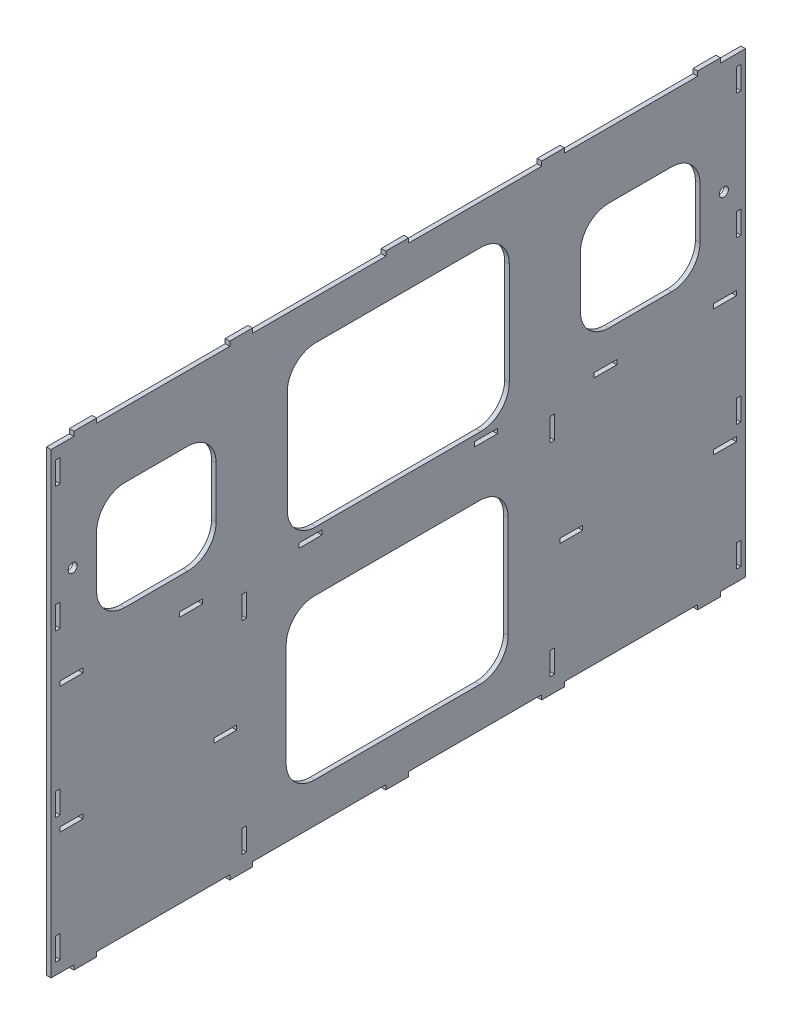
SolidWorks part; units mm, degrees
ref_plane "Front Plane" through (0, 0, 0) normal (0, 0, 1) x (1, 0, 0)
ref_plane "Top Plane" through (0, 0, 0) normal (0, 1, 0) x (1, 0, 0)
ref_plane "Right Plane" through (0, 0, 0) normal (1, 0, 0) x (0, 0, -1)
sketch "Sketch1" plane through (0, 0, 0) normal (1, 0, 0) x (0, 0, -1)
  line L0 (-96.5647, -205) -> (-96.5647, 335.0044) construction
  line L1 (-361.6328, 35) -> (431.039, 35) construction
  line L2 (-401.5647, -166) -> (-381.5647, -166)
  line L3 (-381.5647, 240) -> (-361.5647, 240)
  line L4 (-401.5647, 236) -> (-401.5647, -166)
  line L5 (-381.5647, -170) -> (-361.5647, -170)
  line L7 (208.4353, 236) -> (208.4353, -166)
  line L8 (180.4353, -55) -> (180.4353, -59)
  line L9 (-381.5647, -166) -> (-381.5647, -170)
  line L10 (-361.5647, -166) -> (-361.5647, -170)
  line L11 (-361.5647, -166) -> (-244.5647, -166)
  line L12 (-244.5647, -166) -> (-244.5647, -170)
  line L13 (-224.5647, -166) -> (-224.5647, -170)
  line L14 (-224.5647, -166) -> (-107.5647, -166)
  line L15 (-107.5647, -166) -> (-107.5647, -170)
  line L16 (-87.5647, -170) -> (-87.5647, -166)
  line L17 (-87.5647, -166) -> (29.4353, -166)
  line L18 (29.4353, -166) -> (29.4353, -170)
  line L19 (49.4353, -170) -> (49.4353, -166)
  line L20 (49.4353, -166) -> (166.4353, -166)
  line L21 (166.4353, -166) -> (166.4353, -170)
  line L28 (166.4353, -170) -> (186.4353, -170)
  line L29 (29.4353, -170) -> (49.4353, -170)
  line L30 (-107.5647, -170) -> (-87.5647, -170)
  line L31 (-244.5647, -170) -> (-224.5647, -170)
  line L34 (186.4353, 236) -> (186.4353, 240)
  line L35 (208.4353, 236) -> (186.4353, 236)
  line L37 (49.4353, 236) -> (166.4353, 236)
  line L38 (49.4353, 240) -> (49.4353, 236)
  line L39 (29.4353, 236) -> (29.4353, 240)
  line L40 (-87.5647, 236) -> (29.4353, 236)
  line L41 (-87.5647, 240) -> (-87.5647, 236)
  line L42 (-107.5647, 236) -> (-107.5647, 240)
  line L43 (-224.5647, 236) -> (-107.5647, 236)
  line L44 (-224.5647, 236) -> (-224.5647, 240)
  line L45 (-244.5647, 236) -> (-244.5647, 240)
  line L46 (-361.5647, 236) -> (-361.5647, 240)
  line L47 (-381.5647, 236) -> (-381.5647, 240)
  line L48 (-361.5647, 236) -> (-244.5647, 236)
  line L49 (-401.5647, 236) -> (-381.5647, 236)
  line L50 (166.4353, 236) -> (166.4353, 240)
  line L51 (166.4353, 240) -> (186.4353, 240)
  line L53 (29.4353, 240) -> (49.4353, 240)
  line L54 (-107.5647, 240) -> (-87.5647, 240)
  line L55 (-244.5647, 240) -> (-224.5647, 240)
  line L80 (113.4353, 151.2674) -> (113.4353, 11.421) construction
  line L81 (200.4353, -59) -> (180.4353, -59)
  line L82 (36.8253, 42) -> (36.8253, 22)
  line L83 (36.8253, 22) -> (40.8253, 22)
  line L84 (40.8253, 22) -> (40.8253, 42)
  line L85 (40.8253, 42) -> (36.8253, 42)
  line L86 (36.8253, -136) -> (40.8253, -136)
  line L87 (40.8253, -136) -> (40.8253, -156)
  line L88 (40.8253, -156) -> (36.8253, -156)
  line L89 (36.8253, -156) -> (36.8253, -136)
  line L90 (200.4353, -59) -> (200.4353, -55)
  line L100 (-397.5647, 226) -> (-393.5647, 226)
  line L101 (-393.5647, 116) -> (-393.5647, 96)
  line L102 (-393.5647, 226) -> (-393.5647, 206)
  line L103 (-393.5647, 206) -> (-397.5647, 206)
  line L106 (-393.5647, -46) -> (-393.5647, -26)
  line L108 (-397.5647, -26) -> (-397.5647, -46)
  line L109 (-393.5647, -26) -> (-397.5647, -26)
  line L110 (-397.5647, -136) -> (-397.5647, -156)
  line L111 (-397.5647, -46) -> (-393.5647, -46)
  line L112 (-393.5647, -156) -> (-393.5647, -136)
  line L113 (-393.5647, -136) -> (-397.5647, -136)
  line L116 (-397.5647, 206) -> (-397.5647, 226)
  line L132 (-397.5647, -156) -> (-393.5647, -156)
  line L133 (186.4353, -170) -> (186.4353, -166)
  line L134 (186.4353, -166) -> (208.4353, -166)
  line L135 (-393.5647, 116) -> (-397.5647, 116)
  line L136 (-397.5647, 116) -> (-397.5647, 96)
  line L137 (-397.5647, 96) -> (-393.5647, 96)
  line L138 (204.4353, 206) -> (204.4353, 226)
  line L139 (200.4353, 206) -> (204.4353, 206)
  line L140 (200.4353, 226) -> (200.4353, 206)
  line L141 (204.4353, 226) -> (200.4353, 226)
  line L142 (200.4353, 116) -> (200.4353, 96)
  line L143 (200.4353, 116) -> (204.4353, 116)
  line L144 (204.4353, 116) -> (204.4353, 96)
  line L145 (204.4353, 96) -> (200.4353, 96)
  line L146 (200.4353, -46) -> (200.4353, -26)
  line L147 (204.4353, -46) -> (200.4353, -46)
  line L148 (204.4353, -26) -> (204.4353, -46)
  line L149 (200.4353, -26) -> (204.4353, -26)
  line L150 (204.4353, -156) -> (200.4353, -156)
  line L151 (204.4353, -136) -> (204.4353, -156)
  line L152 (200.4353, -136) -> (204.4353, -136)
  line L153 (200.4353, -156) -> (200.4353, -136)
  line L154 (200.4353, 56) -> (180.4353, 56)
  line L155 (-229.9547, -156) -> (-229.9547, -136)
  line L156 (-233.9547, -156) -> (-229.9547, -156)
  line L157 (-233.9547, -136) -> (-233.9547, -156)
  line L158 (-229.9547, -136) -> (-233.9547, -136)
  line L167 (-233.9547, 42) -> (-229.9547, 42)
  line L168 (-233.9547, 22) -> (-233.9547, 42)
  line L169 (-229.9547, 22) -> (-233.9547, 22)
  line L170 (-229.9547, 42) -> (-229.9547, 22)
  line L171 (200.4353, 56) -> (200.4353, 52)
  line L172 (200.4353, 52) -> (180.4353, 52)
  line L173 (-393.5647, 56) -> (-393.5647, 52)
  line L174 (-373.5647, 56) -> (-373.5647, 52)
  line L175 (-288.5647, 56) -> (-288.5647, 52)
  line L176 (-268.5647, 56) -> (-268.5647, 52)
  line L177 (-183.5647, 56) -> (-183.5647, 52)
  line L178 (-163.5647, 56) -> (-163.5647, 52)
  line L179 (-183.5647, 52) -> (-163.5647, 52)
  line L180 (-183.5647, 56) -> (-163.5647, 56)
  line L181 (-288.5647, 52) -> (-268.5647, 52)
  line L182 (-288.5647, 56) -> (-268.5647, 56)
  line L183 (-393.5647, 52) -> (-373.5647, 52)
  line L184 (-393.5647, 56) -> (-373.5647, 56)
  line L185 (180.4353, 56) -> (180.4353, 52)
  line L186 (95.4353, 56) -> (75.4353, 56)
  line L187 (95.4353, 56) -> (95.4353, 52)
  line L188 (95.4353, 52) -> (75.4353, 52)
  line L189 (75.4353, 56) -> (75.4353, 52)
  line L190 (-9.5647, 56) -> (-29.5647, 56)
  line L191 (-9.5647, 56) -> (-9.5647, 52)
  line L192 (-9.5647, 52) -> (-29.5647, 52)
  line L193 (-29.5647, 56) -> (-29.5647, 52)
  line L194 (-258.5647, -55) -> (-258.5647, -59)
  line L195 (-238.5647, -59) -> (-258.5647, -59)
  line L196 (-238.5647, -59) -> (-238.5647, -55)
  line L197 (-258.5647, -55) -> (-238.5647, -55)
  line L198 (-373.5647, -55) -> (-393.5647, -55)
  line L199 (-393.5647, -59) -> (-393.5647, -55)
  line L200 (-393.5647, -59) -> (-373.5647, -59)
  line L201 (-373.5647, -55) -> (-373.5647, -59)
  line L202 (180.4353, -55) -> (200.4353, -55)
  line L203 (65.4353, -55) -> (45.4353, -55)
  line L204 (45.4353, -59) -> (45.4353, -55)
  line L205 (45.4353, -59) -> (65.4353, -59)
  line L206 (65.4353, -55) -> (65.4353, -59)
  point P4 (-96.5647, 35)
  point P5 (-373.5647, -57)
  point P6 (-258.5647, -57)
  point P97 (40.8253, 32)
  dimension "D5" = 20
  dimension "D6" = 85
  dimension "D7" = 20
  dimension "D8" = 4
  dimension "D9" = 4
  dimension "D10" = 20
  dimension "D11" = 20
  dimension "D12" = 85
  dimension "D13" = 410
  dimension "D14" = 8
  dimension "D15" = 20
  dimension "D16" = 10
  dimension "D17" = 10
  dimension "D18" = 20
  dimension "D19" = 4
  dimension "D20" = 20
  dimension "D21" = 4
  dimension "D22" = 20
  dimension "D23" = 20
  dimension "D24" = 20
  dimension "D25" = 20
  dimension "D26" = 4
  dimension "D27" = 4
  dimension "D28" = 4
  dimension "D29" = 115
  dimension "D30" = 20
  dimension "D31" = 20
  dimension "D32" = 4
  dimension "D33" = 117
  dimension "D34" = 20
  dimension "D35" = 117
  dimension "D36" = 20
  dimension "D37" = 117
  dimension "D38" = 20
  dimension "D39" = 117
  dimension "D40" = 10
  dimension "D41" = 188
  dimension "D43" = 8
  dimension "D45" = 90
  dimension "D46" = 90
extrude "Boss-Extrude1" add sketch "Sketch1" along normal blind 4
sketch "Sketch2" plane through (4, 0, 0) normal (1, 0, 0) x (0, 0, -1)
  line L0 (-401.5647, 131) -> (208.4353, 131) construction
  line L1 (-401.5647, 236) -> (-401.5647, -166) construction
  line L2 (208.4353, -166) -> (208.4353, 236) construction
  line L3 (-97.5647, -170) -> (-97.5647, 240) construction
  line L4 (-107.5647, -170) -> (-87.5647, -170) construction
  line L5 (-87.5647, 240) -> (-107.5647, 240) construction
  line L6 (-87.5647, -166) -> (29.4353, -166) construction
  line L7 (-170.0647, 9) -> (-25.0647, 9)
  line L8 (-195.0647, -16) -> (-195.0647, -106)
  line L9 (-170.0647, -131) -> (-25.0647, -131)
  line L10 (-0.0647, -16) -> (-0.0647, -106)
  line L11 (-195.0647, 9) -> (-0.0647, -131) construction
  line L12 (-195.0647, -131) -> (-0.0647, 9) construction
  line L13 (-169.0647, 201) -> (-24.0647, 201)
  line L14 (-194.0647, 176) -> (-194.0647, 86)
  line L15 (-169.0647, 61) -> (-24.0647, 61)
  line L16 (0.9353, 176) -> (0.9353, 86)
  line L17 (-194.0647, 201) -> (0.9353, 61) construction
  line L18 (-194.0647, 61) -> (0.9353, 201) construction
  line L19 (-336.5647, 178.5) -> (-281.5647, 178.5)
  line L20 (-361.5647, 153.5) -> (-361.5647, 108.5)
  line L21 (-336.5647, 83.5) -> (-281.5647, 83.5)
  line L22 (-256.5647, 153.5) -> (-256.5647, 108.5)
  line L23 (-361.5647, 178.5) -> (-256.5647, 83.5) construction
  line L24 (-361.5647, 83.5) -> (-256.5647, 178.5) construction
  line L25 (88.4353, 178.5) -> (143.4353, 178.5)
  line L26 (63.4353, 153.5) -> (63.4353, 108.5)
  line L27 (88.4353, 83.5) -> (143.4353, 83.5)
  line L28 (168.4353, 153.5) -> (168.4353, 108.5)
  line L29 (63.4353, 178.5) -> (168.4353, 83.5) construction
  line L30 (63.4353, 83.5) -> (168.4353, 178.5) construction
  line L31 (29.4353, 236) -> (-87.5647, 236) construction
  arc A0 (-195.0647, -106) -> (-170.0647, -131) centre (-170.0647, -106) ccw
  arc A1 (-25.0647, -131) -> (-0.0647, -106) centre (-25.0647, -106) ccw
  arc A2 (-170.0647, 9) -> (-195.0647, -16) centre (-170.0647, -16) ccw
  arc A3 (-25.0647, 9) -> (-0.0647, -16) centre (-25.0647, -16) cw
  arc A4 (63.4353, 108.5) -> (88.4353, 83.5) centre (88.4353, 108.5) ccw
  arc A5 (143.4353, 83.5) -> (168.4353, 108.5) centre (143.4353, 108.5) ccw
  arc A6 (143.4353, 178.5) -> (168.4353, 153.5) centre (143.4353, 153.5) cw
  arc A7 (88.4353, 178.5) -> (63.4353, 153.5) centre (88.4353, 153.5) ccw
  arc A8 (-361.5647, 108.5) -> (-336.5647, 83.5) centre (-336.5647, 108.5) ccw
  arc A9 (-336.5647, 178.5) -> (-361.5647, 153.5) centre (-336.5647, 153.5) ccw
  arc A10 (-281.5647, 178.5) -> (-256.5647, 153.5) centre (-281.5647, 153.5) cw
  arc A11 (-281.5647, 83.5) -> (-256.5647, 108.5) centre (-281.5647, 108.5) ccw
  arc A12 (-194.0647, 86) -> (-169.0647, 61) centre (-169.0647, 86) ccw
  arc A13 (-24.0647, 61) -> (0.9353, 86) centre (-24.0647, 86) ccw
  arc A14 (-24.0647, 201) -> (0.9353, 176) centre (-24.0647, 176) cw
  arc A15 (-169.0647, 201) -> (-194.0647, 176) centre (-169.0647, 176) ccw
  point P12 (-97.5647, -61)
  point P17 (-96.5647, 131)
  point P22 (-309.0647, 131)
  point P27 (115.9353, 131)
  point P32 (-0.0647, -61)
  dimension "D11" = 25
  dimension "D1" = 195
  dimension "D2" = 195
  dimension "D3" = 140
  dimension "D4" = 140
  dimension "D5" = 105
  dimension "D6" = 95
  dimension "D7" = 95
  dimension "D8" = 105
  dimension "D9" = 40
  dimension "D10" = 40
  dimension "D12" = 35
  dimension "D13" = 35
extrude "Cut-Extrude1" cut sketch "Sketch2" against normal blind 10
sketch "Sketch3" plane through (4, 0, 0) normal (1, 0, 0) x (0, 0, -1)
  line L0 (-401.5647, 136.4778) -> (227.3683, 136.4778) construction
  line L1 (-401.5647, 236) -> (-401.5647, -166) construction
  line L3 (-361.5647, 153.5) -> (-361.5647, 108.5) construction
  line L4 (168.4353, 108.5) -> (168.4353, 153.5) construction
  circle A0 centre (-382.5647, 136.4778) radius 4
  circle A1 centre (189.4353, 136.4778) radius 4
  dimension "D1" = 8
  dimension "D2" = 8
  dimension "D3" = 21
  dimension "D4" = 21
extrude "Cut-Extrude2" cut sketch "Sketch3" against normal blind 10
